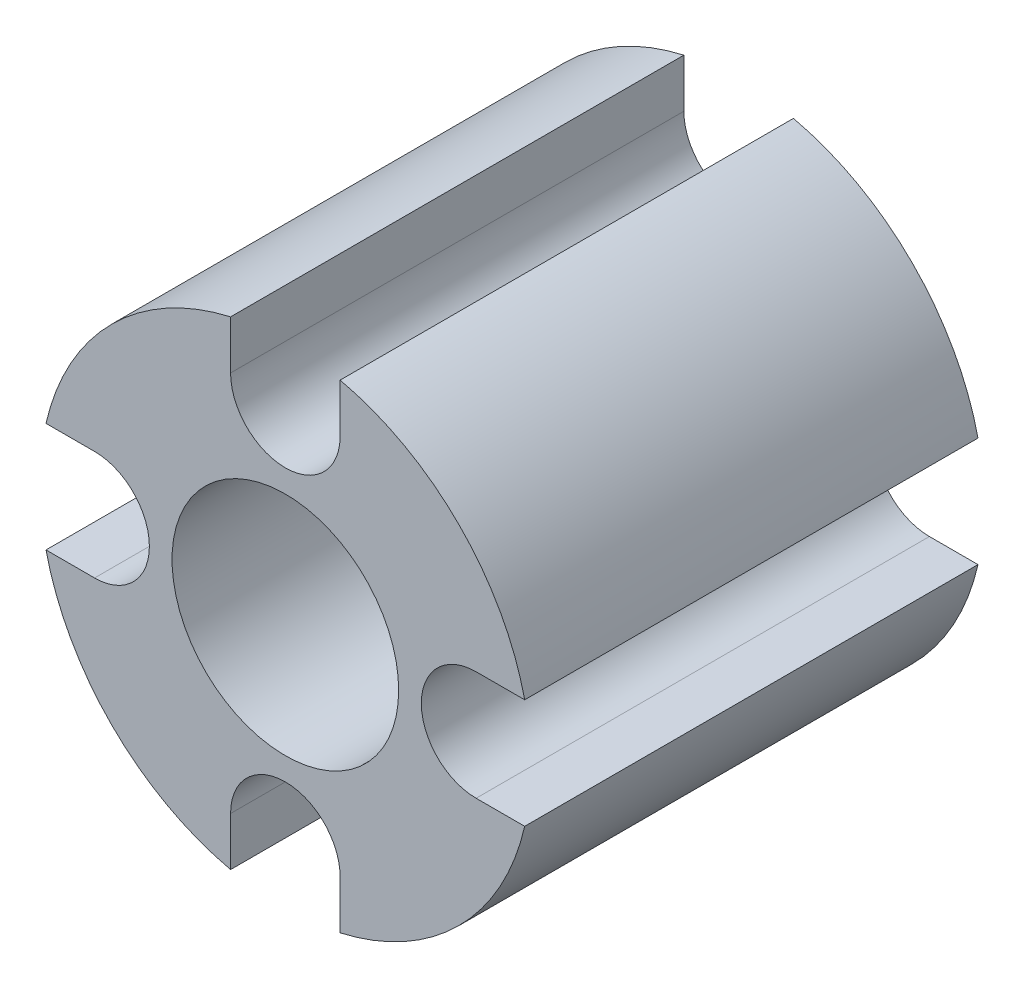
SolidWorks part; units mm, degrees
ref_plane "Plan de face" through (0, 0, 0) normal (0, 0, 1) x (1, 0, 0)
ref_plane "Plan de dessus" through (0, 0, 0) normal (0, 1, 0) x (1, 0, 0)
ref_plane "Plan de droite" through (0, 0, 0) normal (1, 0, 0) x (0, 0, -1)
sketch "Esquisse1" plane through (0, 0, 0) normal (0, 0, 1) x (1, 0, 0)
  line L0 (-0.725, 2.525) -> (-0.725, 3.1681)
  line L1 (0.725, 2.525) -> (0.725, 3.1681)
  line L2 (2.525, 0.725) -> (3.1681, 0.725)
  line L3 (2.525, -0.725) -> (3.1681, -0.725)
  line L4 (0.725, -2.525) -> (0.725, -3.1681)
  line L5 (-0.725, -2.525) -> (-0.725, -3.1681)
  line L6 (-2.525, -0.725) -> (-3.1681, -0.725)
  line L7 (-2.525, 0.725) -> (-3.1681, 0.725)
  arc A0 (-0.725, 3.1681) -> (-3.1681, 0.725) centre (0, 0) ccw
  circle A1 centre (0, 0) radius 1.5
  arc A2 (-0.725, 2.525) -> (0.725, 2.525) centre (0, 2.525) ccw
  arc A3 (2.525, 0.725) -> (2.525, -0.725) centre (2.525, 0) ccw
  arc A4 (0.725, -2.525) -> (-0.725, -2.525) centre (0, -2.525) ccw
  arc A5 (-2.525, -0.725) -> (-2.525, 0.725) centre (-2.525, 0) ccw
  arc A6 (-3.1681, -0.725) -> (-0.725, -3.1681) centre (0, 0) ccw
  arc A7 (0.725, -3.1681) -> (3.1681, -0.725) centre (0, 0) ccw
  arc A8 (3.1681, 0.725) -> (0.725, 3.1681) centre (0, 0) ccw
  point P26 (0, 0)
  dimension "D1" = 6.5
  dimension "D2" = 3
  dimension "D3" = 1.45
  dimension "D4" = 4
extrude "Boss.-Extru.2" add sketch "Esquisse1" along normal blind 6
